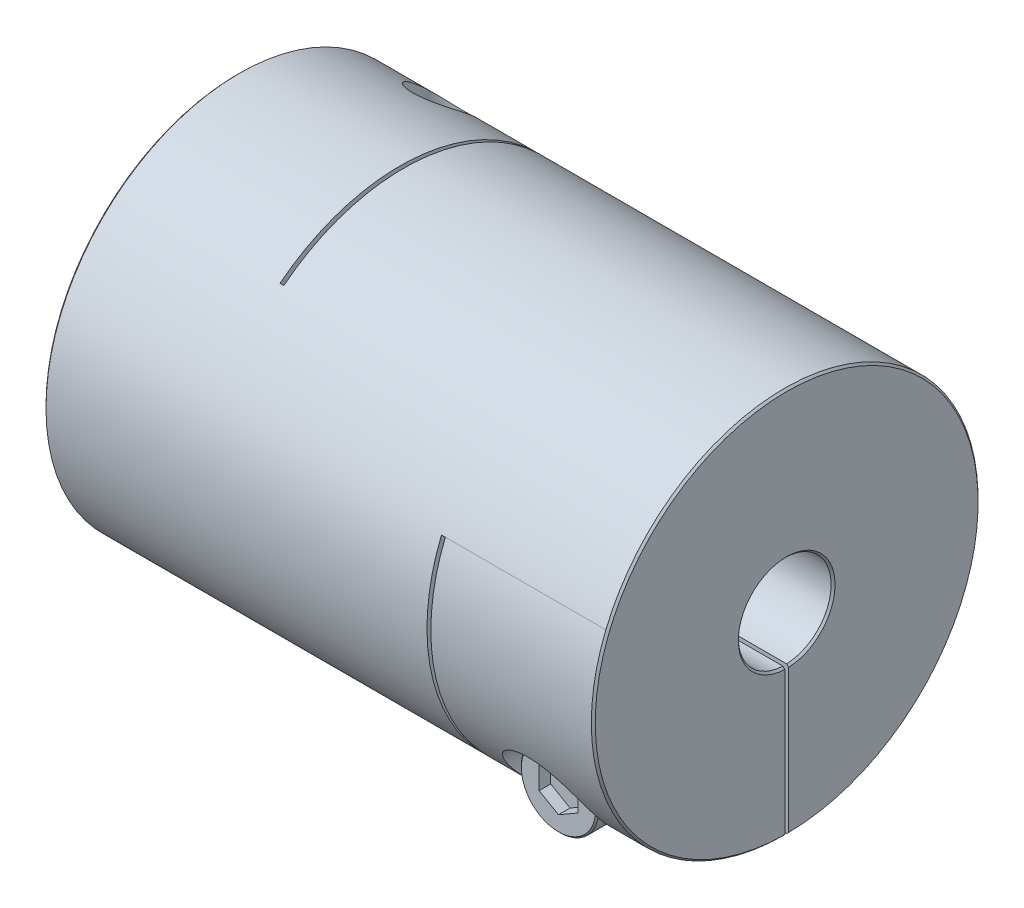
SolidWorks part; units mm, degrees
ref_plane "Front Plane" through (0, 0, 0) normal (0, 0, 1) x (1, 0, 0)
ref_plane "Top Plane" through (0, 0, 0) normal (0, 1, 0) x (1, 0, 0)
ref_plane "Right Plane" through (0, 0, 0) normal (1, 0, 0) x (0, 0, -1)
sketch "Sketch1" plane through (0, 0, 0) normal (1, 0, 0) x (0, 0, -1)
  circle A0 centre (0, 0) radius 25
  dimension "dim D" = 50
extrude "Boss-Extrude1" add sketch "Sketch1" along normal mid plane 71
sketch "Sketch2" plane through (35.5, 0, 0) normal (1, 0, 0) x (0, 0, -1)
  circle A0 centre (0, 0) radius 6
  dimension "dim D1" = 12
extrude "Cut-Extrude1" cut sketch "Sketch2" against normal through all
chamfer "Chamfer1" distance 0.254 angle 45 4 edges at (-35.5, 0, -6) (-35.5, 0, -25) (35.5, 0, -25) (35.5, 0, -6)
ref_plane "Plane2" through (0, -25, 0) normal (0, -1, 0) x (1, 0, 0)
ref_plane "L1" through (-25, 0, 0) normal (-1, 0, 0) x (0, 0, 1)
sketch "Sketch4" plane through (0, -25, 0) normal (0, -1, 0) x (1, 0, 0)
  line L0 (-35.246, -25) -> (35.246, -25) construction
  line L1 (-14.5, -25) -> (-14, -25)
  line L2 (-14.5, -25) -> (-14.5, 15.5)
  line L3 (-14.5, 15.5) -> (-14, 15.5)
  line L4 (-14, -25) -> (-14, 15.5)
  line L5 (-14.5, 6) -> (-14.5, 25) construction
  line L6 (35.246, 6) -> (-35.246, 6) construction
  line L7 (35.246, 25) -> (-35.246, 25) construction
  line L10 (-14.5, 15.5) -> (-35.5, 15.5) construction
  line L11 (-35.5, 24.746) -> (-35.5, -24.746) construction
  line L12 (-25, 10.2256) -> (-25, -10.2256) construction
  point P16 (-25, 15.5)
  dimension "D1" = 0.5
extrude "Cut-Extrude2" cut sketch "Sketch4" against normal through all
ref_plane "Plane4" through (0, 0, -25) normal (0, 0, -1) x (-1, 0, 0)
sketch "Sketch7" plane through (0, 0, -25) normal (0, 0, -1) x (-1, 0, 0)
  line L1 (-14, -25) -> (-14.5, -25)
  line L2 (-14.5, -25) -> (-14.5, 9.5)
  line L3 (-14.5, 9.5) -> (-14, 9.5)
  line L4 (-14, -25) -> (-14, 9.5)
  line L5 (35.5, 8.6487) -> (25, 8.6487) construction
  line L7 (-10.505, -25) -> (10.505, -25) construction
  line L8 (-35.246, -6) -> (14, -6) construction
  line L9 (35.5, -24.746) -> (35.5, 24.746) construction
  line L10 (-35.246, -6) -> (14, -6) construction
  line L11 (14, 19.615) -> (14.5, 19.615) construction
  line L12 (-14.5, 9.5) -> (-14.5, -25) construction
  line L14 (-35.246, -6) -> (14, -6) construction
  line L16 (-35.246, -6) -> (14, -6) construction
  line L17 (14.5, -25) -> (35.246, -25) construction
  line L18 (25, -10.2256) -> (25, 10.2256) construction
  line L19 (-35.246, -25) -> (-35.246, 25) construction
  line L20 (-35.5, 9.5) -> (-25, 9.5) construction
  line L21 (-35.5, 24.746) -> (-35.5, -24.746) construction
  line L22 (-25, 9.5) -> (-14.5, 9.5) construction
  line L23 (-35.246, -25) -> (-35.246, 25) construction
  line L24 (-35.246, -6) -> (-35.246, 25) construction
  line L25 (-35.246, -6) -> (14, -6) construction
  point P23 (-14.5, 9.5)
  point P33 (-35.246, 9.5)
extrude "Cut-Extrude3" cut sketch "Sketch7" against normal through all
sketch "Sketch8" plane through (0, 0, 0) normal (0, 1, 0) x (1, 0, 0)
  line L0 (-14.5, -15.5) -> (-14.5, 25) construction
  line L1 (-35.5, 25) -> (-14.5, 25)
  line L2 (-35.5, 25) -> (-35.5, 0)
  line L3 (-35.5, 0) -> (-14.5, 0)
  line L4 (-14.5, 25) -> (-14.5, 0)
  line L5 (10.505, 25) -> (-10.505, 25) construction
  line L6 (-35.5, 24.746) -> (-35.5, -24.746) construction
extrude "Cut-Extrude5" cut sketch "Sketch8" against normal mid plane 0.5
sketch "Sketch13" plane through (0, 0, 0) normal (0, 0, 1) x (1, 0, 0)
  line L0 (35.5, -24.746) -> (35.5, 24.746) construction
  line L1 (14.5, -25) -> (35.5, -25)
  line L2 (14.5, -25) -> (14.5, 0)
  line L3 (14.5, 0) -> (35.5, 0)
  line L4 (35.5, -25) -> (35.5, 0)
extrude "Cut-Extrude6" cut sketch "Sketch13" against normal mid plane 0.5
hole_wizard "CBORE for M6 SHCS1" positions "Sketch12" profile "Sketch11" counterbore size "M6" standard "Ansi Metric" end condition through all
sketch "Sketch12" plane through (0, -25, 0) normal (0, -1, 0) x (1, 0, 0)
  line L0 (-25, 10.2256) -> (-25, -10.2256) construction
  line L1 (-14.5, -5.9948) -> (-14.5, -24.9987) construction
  line L2 (-14.5, -5.9948) -> (-14.5, -24.9987)
  line L3 (-14.5, -15.4968) -> (-25, -15.4968) construction
  point P0 (-25, -15.4968)
sketch "Sketch11" plane through (-25, -25, -15.4968) normal (1, 0, 0) x (0, 0, -1)
  line L0 (0, 0) -> (0, 50)
  line L1 (0, 50) -> (3.3, 50)
  line L3 (3.3, 50) -> (3.3, 12)
  line L4 (3.3, 12) -> (5.5, 12)
  line L5 (5.5, 12) -> (5.5, 0)
  line L7 (5.5, 0) -> (0, 0)
  line L11 (0, -6.35) -> (0, 107.95) construction
  dimension "Thru Hole Dia." = 6.6
  dimension "Thru Hole Depth" = 50
  dimension "C'Bore Dia." = 11
  dimension "C'Bore Depth" = 12
ref_plane "Plane5" through (0, 0, 25) normal (0, 0, 1) x (1, 0, 0)
hole_wizard "CBORE for M6 SHCS2" positions "Sketch15" profile "Sketch14" counterbore size "M6" standard "Ansi Metric" end condition through all
sketch "Sketch15" plane through (0, 0, 25) normal (0, 0, 1) x (1, 0, 0)
  line L0 (-30.5, -13) -> (-19.5, -13) construction
  line L1 (-30.5, -13) -> (-19.5, -13)
  line L5 (0, 0) -> (0, 25) construction
  line L6 (-14.5, 25) -> (-35.246, 25) construction
  line L8 (30.5, -13) -> (19.5, -13)
  line L9 (25, -13) -> (25, -15.4968) construction
  line L11 (25, -24.9987) -> (25, -5.9948) construction
  line L12 (35.246, -24.9987) -> (14.5, -24.9987) construction
  line L13 (14.5, -5.9948) -> (35.246, -5.9948) construction
  point P0 (25, -15.4968)
sketch "Sketch14" plane through (25, -15.4968, 25) normal (1, 0, 0) x (0, -1, 0)
  line L0 (0, 0) -> (0, 50)
  line L1 (0, 50) -> (3.3, 50)
  line L3 (3.3, 50) -> (3.3, 12)
  line L4 (3.3, 12) -> (5.5, 12)
  line L5 (5.5, 12) -> (5.5, 0)
  line L7 (5.5, 0) -> (0, 0)
  line L11 (0, -6.35) -> (0, 107.95) construction
  dimension "Thru Hole Dia." = 6.6
  dimension "Thru Hole Depth" = 50
  dimension "C'Bore Dia." = 11
  dimension "C'Bore Depth" = 12
sketch "Sketch16" plane through (0, 0, 13) normal (0, 0, 1) x (1, 0, 0)
  circle A0 centre (25, -15.4968) radius 5
  dimension "screw dia" = 10
extrude "Boss-Extrude2" add sketch "Sketch16" along normal blind 6 separate body
sketch "Sketch17" plane through (0, 0, 13) normal (0, 0, -1) x (-1, 0, 0)
  circle A0 centre (-25, -15.4968) radius 1
  dimension "D1" = 2
extrude "Boss-Extrude3" add sketch "Sketch17" along normal blind 6.5
chamfer "Chamfer2" distance 0.2 angle 45 3 edges at (24, -15.4968, 6.5) (30, -15.4968, 13) (30, -15.4968, 19)
sketch "Sketch18" plane through (0, 0, 19) normal (0, 0, 1) x (1, 0, 0)
  line L1 (25, -18.3835) -> (27.5, -16.9401)
  line L2 (27.5, -16.9401) -> (27.5, -14.0534)
  line L3 (27.5, -14.0534) -> (25, -12.61)
  line L4 (25, -12.61) -> (22.5, -14.0534)
  line L5 (22.5, -14.0534) -> (22.5, -16.9401)
  line L6 (22.5, -16.9401) -> (25, -18.3835)
  circle A0 centre (25, -15.4968) radius 2.5 construction
  dimension "hex" = 5
extrude "Cut-Extrude7" cut sketch "Sketch18" against normal blind 1.5
mirror "Mirror1" about plane through (0, 0, 0) normal (1, 0, 0) of bodies 121
pattern_circular "CirPattern1" count 2 every 90 about axis through (0, 0, 0) along (1, 0, 0) of bodies 122
delete or keep bodies "Body-Delete1" type delete bodies bodies 122
